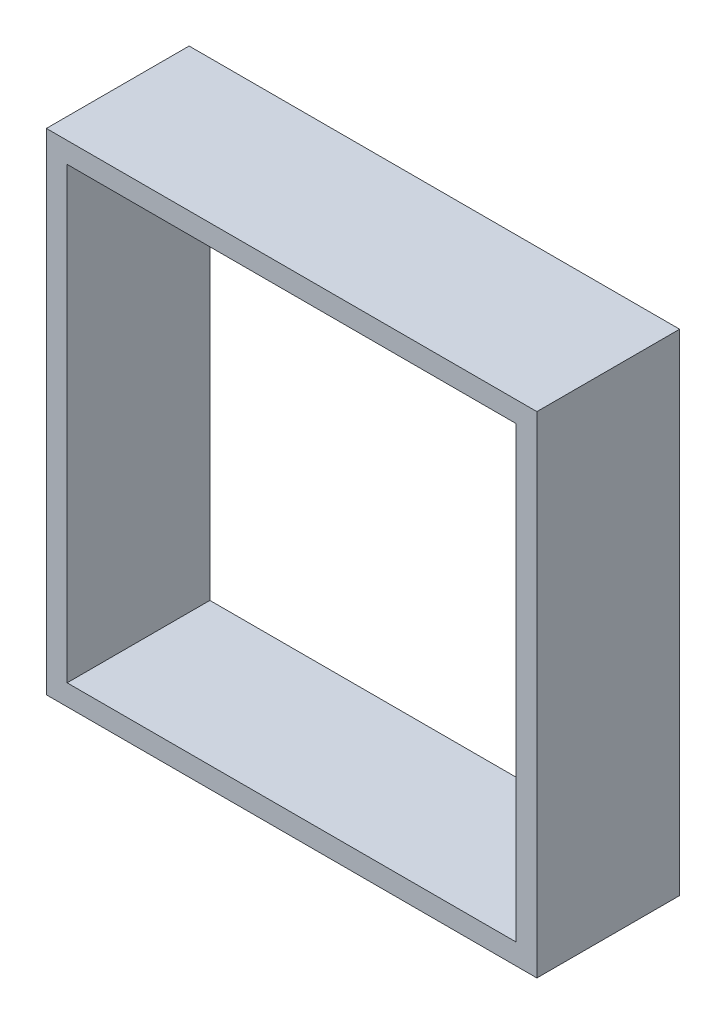
SolidWorks part; units mm, degrees
ref_plane "Front Plane" through (0, 0, 0) normal (0, 0, 1) x (1, 0, 0)
ref_plane "Top Plane" through (0, 0, 0) normal (0, 1, 0) x (1, 0, 0)
ref_plane "Right Plane" through (0, 0, 0) normal (1, 0, 0) x (0, 0, -1)
sketch "Sketch1" plane through (0, 0, 0) normal (0, 0, 1) x (1, 0, 0)
  line L1 (-9.45, -9.45) -> (9.45, -9.45)
  line L2 (-9.45, -9.45) -> (-9.45, 9.45)
  line L3 (-9.45, 9.45) -> (9.45, 9.45)
  line L4 (9.45, -9.45) -> (9.45, 9.45)
  line L5 (-9.45, -9.45) -> (9.45, 9.45) construction
  line L6 (-9.45, 9.45) -> (9.45, -9.45) construction
  line L7 (-8.65, -8.65) -> (8.65, -8.65)
  line L8 (-8.65, -8.65) -> (-8.65, 8.65)
  line L9 (-8.65, 8.65) -> (8.65, 8.65)
  line L10 (8.65, -8.65) -> (8.65, 8.65)
  line L11 (-8.65, -8.65) -> (8.65, 8.65) construction
  line L12 (-8.65, 8.65) -> (8.65, -8.65) construction
  point P0 (0, 0)
  point P6 (0, 0)
  dimension "D1" = 18.9
  dimension "D2" = 0.8
extrude "Boss-Extrude1" add sketch "Sketch1" along normal blind 5.5
